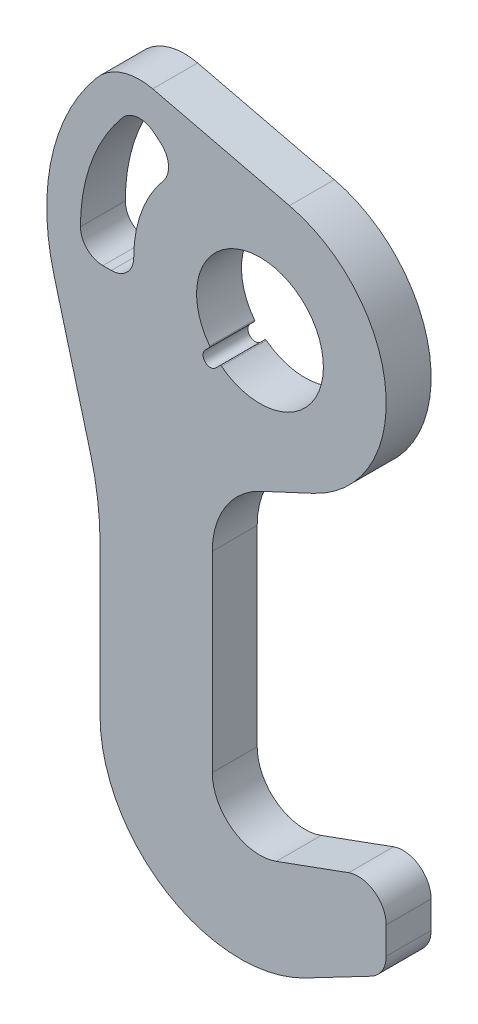
SolidWorks part; units mm, degrees
ref_plane "Plane1" through (0, 0, 0) normal (0, 0, 1) x (1, 0, 0)
ref_plane "Plane2" through (0, 0, 0) normal (0, 1, 0) x (1, 0, 0)
ref_plane "Plane3" through (0, 0, 0) normal (1, 0, 0) x (0, 0, -1)
sketch "Sketch1" plane through (0, 0, 0) normal (0, 0, 1) x (1, 0, 0)
  line L0 (0, 0) -> (0, -145) construction
  line L1 (5.8143, -160.9748) -> (31.5798, -151.5969)
  line L2 (-17, -145) -> (-17, -76.6913)
  line L3 (0.3215, -49.5021) -> (19.0178, -40.7839)
  line L4 (-73.4104, -19.6702) -> (-60.4074, -68.1979)
  line L5 (39.6385, -179.5196) -> (16.1927, -191.7956)
  line L6 (-57, -147.5) -> (-57, -94.0798)
  line L7 (0, 0) -> (-17.7464, -17.7464) construction
  line L8 (10.4938, 43.7594) -> (-38.2346, 55.4447)
  line L9 (45, -160.9938) -> (45, -170.6605)
  line L10 (-15.8215, -19.5338) -> (-14.266, -17.9783)
  line L11 (0, 0) -> (-76.6044, 64.2788) construction
  line L12 (-19.5338, -15.8215) -> (-17.9783, -14.266)
  line L13 (0, 0) -> (-42.2862, 15.3909) construction
  line L15 (-53, -8) -> (-56, -8)
  line L16 (0, 0) -> (-100, 0) construction
  line L17 (-35.4581, 40.1961) -> (-37.7562, 42.1245)
  arc A0 (-13.74, -17.9436) -> (-17.9436, -13.74) centre (0, 0) ccw
  arc A1 (19.0178, -40.7839) -> (10.4938, 43.7594) centre (0, 0) ccw
  arc A2 (-17, -145) -> (5.8143, -160.9748) centre (0, -145) ccw
  arc A3 (-57, -147.5) -> (16.1927, -191.7956) centre (-7, -147.5) ccw
  arc A4 (-17, -76.6913) -> (0.3215, -49.5021) centre (13, -76.6913) cw
  arc A5 (-73.4104, -19.6702) -> (-58.2194, 48.8519) centre (0, 0) cw
  arc A6 (31.5798, -151.5969) -> (45, -160.9938) centre (35, -160.9938) cw
  arc A7 (45, -170.6605) -> (39.6385, -179.5196) centre (35, -170.6605) cw
  arc A8 (-60.4074, -68.1979) -> (-57, -94.0798) centre (-157, -94.0798) cw
  arc A9 (-64, 0) -> (-56, -8) centre (-56, 0) ccw
  arc A10 (-35.4581, 40.1961) -> (-34.472, 28.9254) centre (-40.6004, 34.0677) cw
  arc A11 (-49.0268, 41.1384) -> (-37.7562, 42.1245) centre (-42.8985, 35.9961) cw
  arc A12 (-34.472, 28.9254) -> (-45, 0) centre (0, 0) ccw
  arc A13 (-53, -8) -> (-45, 0) centre (-53, 0) ccw
  arc A14 (-14.266, -17.9783) -> (-13.74, -17.9436) centre (-13.9832, -18.2612) cw
  arc A15 (-58.2194, 48.8519) -> (-38.2346, 55.4447) centre (-42.8985, 35.9961) cw
  arc A16 (-15.8215, -19.5338) -> (-19.5338, -15.8215) centre (-17.6777, -17.6777) cw
  arc A17 (-49.0268, 41.1384) -> (-64, 0) centre (0, 0) ccw
  arc A18 (-17.9783, -14.266) -> (-17.9436, -13.74) centre (-18.2612, -13.9832) ccw
  point P19 (-17, -57.5792)
  point P25 (45, -146.7124)
  point P28 (45, -176.7124)
  point P34 (-28.7806, 34.593)
  point P52 (-14.0163, -17.7286)
  point P62 (-17.7286, -14.0163)
  dimension "D1" = 45
  dimension "D2" = 45.2
  dimension "D3" = 17
  dimension "D13" = 76
  dimension "D15" = 30
  dimension "D16" = 8
  dimension "D6" = 10
  dimension "D17" = 2.5
  dimension "D20" = 8
  dimension "D21" = 15
  dimension "D23" = 5.25
  dimension "D11" = 8
  dimension "D8" = 50
  dimension "D22" = 100
  dimension "D12" = 8
  dimension "D26" = 0.4
  dimension "D27" = 64
  dimension "D4" = 145
  dimension "D5" = 65
  dimension "D7" = 70
  dimension "D9" = 40
  dimension "D10" = 45
  dimension "D14" = 30
  dimension "D19" = 20
  dimension "D24" = 25
  dimension "D25" = 45
extrude "Base-Extrude" add sketch "Sketch1" along normal blind 16
sketch "Sketch3" [suppressed] plane through (0, 0, 0) normal (0, 0, -1) x (-1, 0, 0)
  line L0 (0, 0) -> (0, -66) construction
  line L1 (0, -66) -> (21, -66) construction
  line L2 (21, -66) -> (0, 0) construction
  dimension "D1" = 66
  dimension "D2" = 21
  dimension "D3" = 17.65
